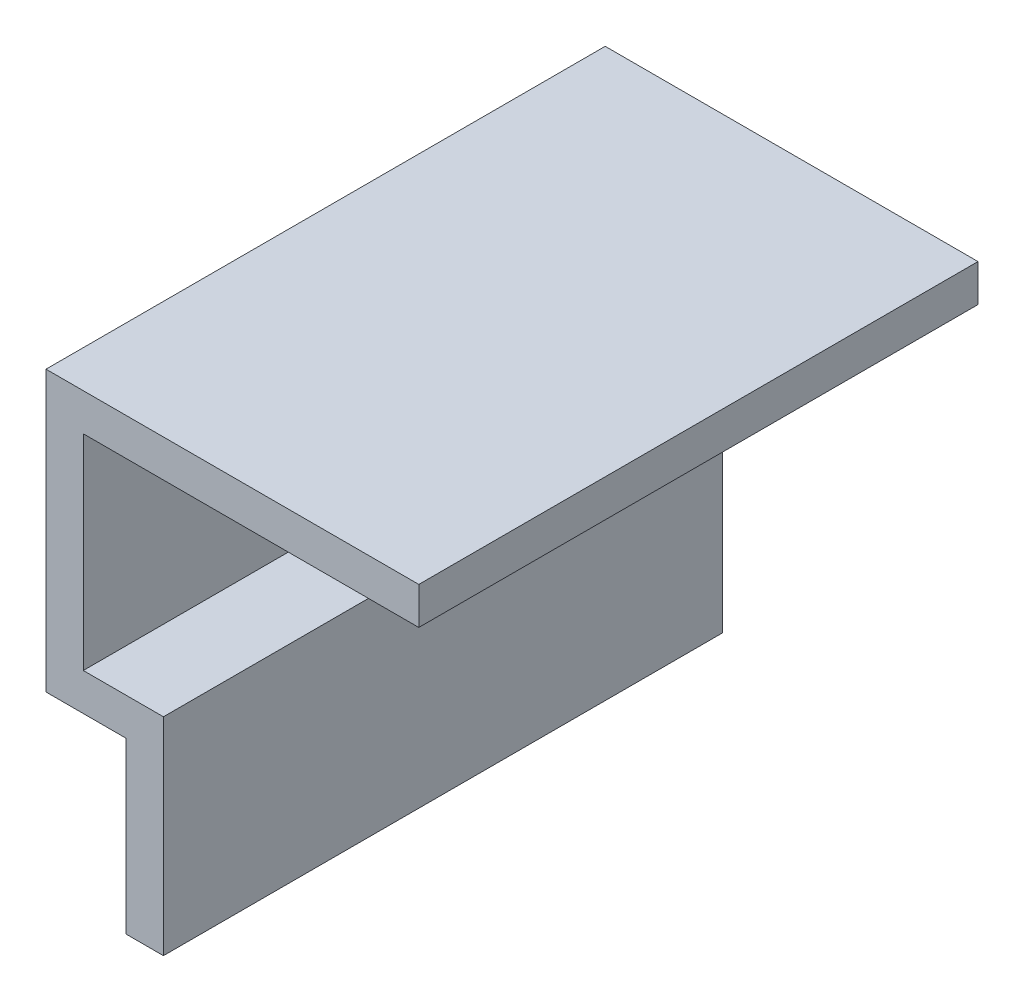
SolidWorks part; units mm, degrees
ref_plane "前视基准面" through (0, 0, 0) normal (0, 0, 1) x (1, 0, 0)
ref_plane "上视基准面" through (0, 0, 0) normal (0, 1, 0) x (1, 0, 0)
ref_plane "右视基准面" through (0, 0, 0) normal (1, 0, 0) x (0, 0, -1)
sketch "草图1" plane through (0, 0, 0) normal (0, 0, 1) x (1, 0, 0)
  line L0 (-28.9502, -18.1907) -> (-28.9502, -9.0907)
  line L1 (-28.9502, -9.0907) -> (-33.2502, -9.0907)
  line L2 (-33.2502, -9.0907) -> (-33.2502, 5.9093)
  line L3 (-33.2502, 5.9093) -> (-13.2502, 5.9093)
  line L4 (-13.2502, 5.9093) -> (-13.2502, 3.9093)
  line L5 (-13.2502, 3.9093) -> (-31.2502, 3.9093)
  line L6 (-31.2502, 3.9093) -> (-31.2502, -7.0907)
  line L7 (-31.2502, -7.0907) -> (-26.9502, -7.0907)
  line L8 (-26.9502, -7.0907) -> (-26.9502, -18.1907)
  line L9 (-26.9502, -18.1907) -> (-28.9502, -18.1907)
extrude "凸台-拉伸1" add sketch "草图1" along normal blind 30
